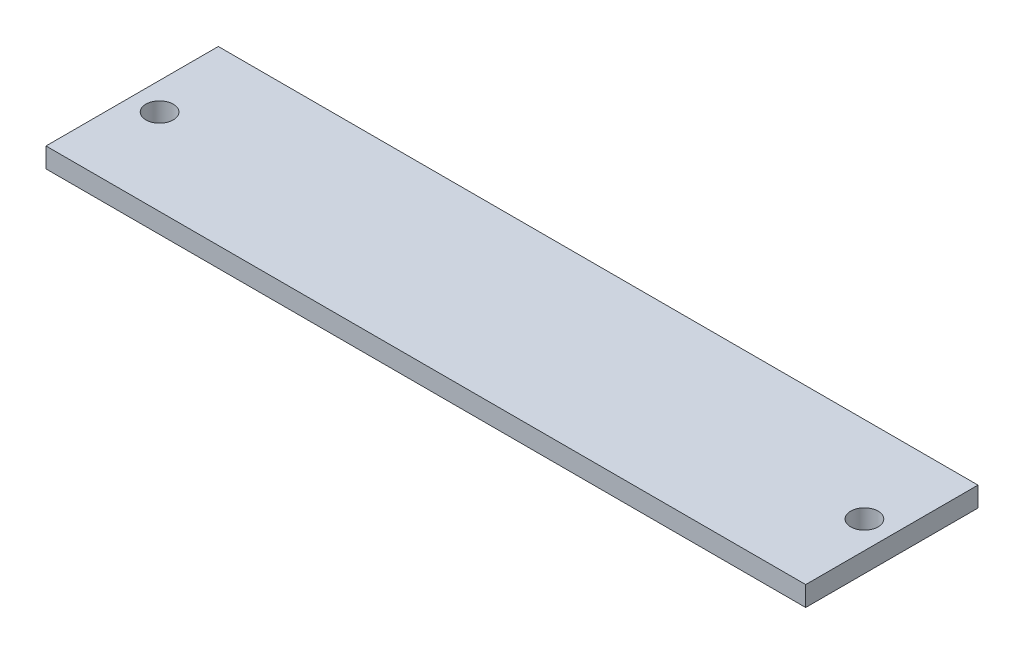
SolidWorks part; units mm, degrees
ref_plane "Front Plane" through (0, 0, 0) normal (0, 0, 1) x (1, 0, 0)
ref_plane "Top Plane" through (0, 0, 0) normal (0, 1, 0) x (1, 0, 0)
ref_plane "Right Plane" through (0, 0, 0) normal (1, 0, 0) x (0, 0, -1)
sketch "Sketch2" plane through (0, 0, 0) normal (0, 1, 0) x (1, 0, 0)
  line L0 (0, 11) -> (0, -11) construction
  line L1 (-48.5, -11) -> (48.5, -11)
  line L2 (-48.5, -11) -> (-48.5, 11)
  line L3 (-48.5, 11) -> (48.5, 11)
  line L4 (48.5, -11) -> (48.5, 11)
  line L5 (-48.5, -11) -> (48.5, 11) construction
  line L6 (-48.5, 11) -> (48.5, -11) construction
  circle A0 centre (45, 0) radius 1.75
  circle A1 centre (-45, 0) radius 1.75
  point P0 (0, 0)
  point P10 (0, 0)
  point P11 (48.5, 0)
  dimension "D3" = 3.5
  dimension "D1" = 97
  dimension "D2" = 22
  dimension "D4" = 45
extrude "Boss-Extrude1" add sketch "Sketch2" along normal blind 2.54
